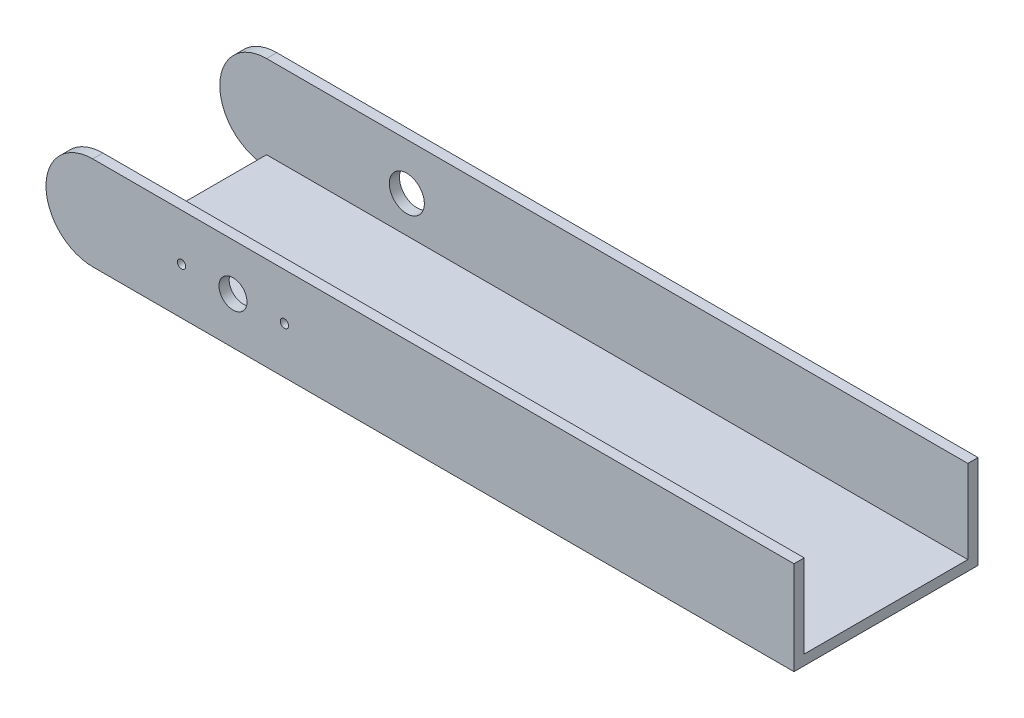
SolidWorks part; units mm, degrees
ref_plane "Front Plane" through (0, 0, 0) normal (0, 0, 1) x (1, 0, 0)
ref_plane "Top Plane" through (0, 0, 0) normal (0, 1, 0) x (1, 0, 0)
ref_plane "Right Plane" through (0, 0, 0) normal (1, 0, 0) x (0, 0, -1)
sketch "Sketch1" plane through (0, 0, 0) normal (0, 0, 1) x (1, 0, 0)
  line L1 (0, 0) -> (190.5, 0)
  line L3 (0, 25.4) -> (190.5, 25.4)
  line L4 (190.5, 0) -> (190.5, 25.4)
  arc A0 (0, 25.4) -> (0, 0) centre (0, 12.7) ccw
  point P6 (-12.7, 12.7)
  dimension "D3" = 12.7
  dimension "D1" = 203.2
  dimension "D2" = 25.4
extrude "Boss-Extrude1" add sketch "Sketch1" along normal blind 2.7686
sketch "Sketch3" plane through (0, 0, 2.7686) normal (0, 0, 1) x (1, 0, 0)
  line L0 (-12.7, 12.7) -> (190.5, 12.7) construction
  line L2 (190.5, 0) -> (190.5, 25.4) construction
  circle A0 centre (38.1, 12.7) radius 3.81
  arc A1 (0, 25.4) -> (0, 0) centre (0, 12.7) ccw construction
  circle A2 centre (24.13, 12.7) radius 1.1303
  circle A3 centre (52.07, 12.7) radius 1.1303
  point P13 (0, 0)
  point P14 (22.959, 12.7)
  point P15 (0, 0)
  point P16 (51.9438, 12.7)
  dimension "D2" = 7.62
  dimension "D3" = 2.2606
  dimension "D4" = 2.2606
  dimension "D1" = 50.8
  dimension "D5" = 27.94
  dimension "D6" = 13.97
extrude "Cut-Extrude1" cut sketch "Sketch3" against normal through all
sketch "Sketch5" plane through (0, 0, 2.7686) normal (0, 0, 1) x (1, 0, 0)
  line L0 (190.5, 0) -> (190.5, 25.4) construction
  line L1 (0, 0) -> (190.5, 0)
  line L2 (0, 0) -> (0, 2.7686)
  line L3 (0, 2.7686) -> (190.5, 2.7686)
  line L4 (190.5, 0) -> (190.5, 2.7686)
  line L5 (0, 0) -> (190.5, 0) construction
  dimension "D1" = 2.7686
  dimension "D2" = 190.5
extrude "Boss-Extrude2" add sketch "Sketch5" against normal blind 44.45 from surface at -2.7686 starting at face at (25.2603, 12.7, 0)
sketch "Sketch6" plane through (0, 0, -44.45) normal (0, 0, -1) x (-1, 0, 0)
  line L0 (-190.5, 2.7686) -> (-190.5, 25.4) construction
  line L1 (12.7, 12.7) -> (-190.5, 12.7) construction
  line L3 (0, 25.4) -> (-190.5, 25.4)
  line L4 (-190.5, 12.7) -> (-190.5, 25.4)
  line L5 (-190.5, 12.7) -> (-190.5, 0)
  line L6 (-190.5, 0) -> (0, 0)
  arc A1 (0, 0) -> (0, 25.4) centre (0, 12.7) ccw construction
  arc A3 (0, 0) -> (0, 25.4) centre (0, 12.7) ccw construction
  arc A4 (0, 25.4) -> (0, 0) centre (0, 12.7) cw
extrude "Boss-Extrude3" add sketch "Sketch6" along normal blind 2.7686
sketch "Sketch7" plane through (0, 0, -47.2186) normal (0, 0, -1) x (-1, 0, 0)
  line L1 (-190.5, 12.7) -> (12.7, 12.7) construction
  line L2 (-190.5, 25.4) -> (-190.5, 0) construction
  arc A0 (0, 0) -> (0, 25.4) centre (0, 12.7) ccw construction
  circle A1 centre (-38.1, 12.7) radius 4.7625
  dimension "D1" = 9.525
  dimension "D2" = 50.8
extrude "Cut-Extrude2" cut sketch "Sketch7" against normal up to surface (2.7686 mm away) from surface at 0 up to face at (73.66, 11.2674, -44.45) starting at face at (92.075, 12.7, -47.2186)
